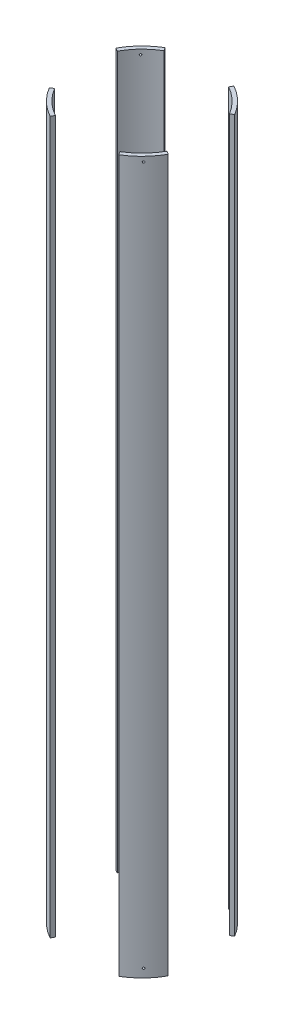
SolidWorks part; units mm, degrees
material "6061-T6 (SS)"
ref_plane "Front Plane" through (0, 0, 0) normal (0, 0, 1) x (1, 0, 0)
ref_plane "Top Plane" through (0, 0, 0) normal (0, 1, 0) x (1, 0, 0)
ref_plane "Right Plane" through (0, 0, 0) normal (1, 0, 0) x (0, 0, -1)
sketch "Sketch2" plane through (0, 0, 0) normal (0, 1, 0) x (1, 0, 0)
  circle A0 centre (0, 0) radius 88.9
  circle A1 centre (0, 0) radius 83.82
  dimension "D1" = 177.8
  dimension "D2" = 167.64
extrude "Boss-Extrude1" add sketch "Sketch2" along normal mid plane 935.896
sketch "Sketch3" plane through (0, 0, 0) normal (0, 1, 0) x (1, 0, 0)
  line L0 (0, 0) -> (169.6618, 101.6776)
  line L1 (-58.1167, 96.9749) -> (0, 0)
  line L2 (0, 0) -> (53.9, 96.9749)
  line L3 (53.9, 96.9749) -> (-58.1167, 96.9749)
  line L4 (0, 0) -> (70.9917, -118.4586)
  line L5 (70.9917, -118.4586) -> (-65.8409, -118.4586)
  line L6 (-65.8409, -118.4586) -> (0, 0)
  line L7 (169.6618, 101.6776) -> (169.6618, -94.3004)
  line L8 (169.6618, -94.3004) -> (0, 0)
  line L9 (0, 0) -> (-123.7413, 68.7771)
  line L10 (-123.7413, 68.7771) -> (-123.7413, -74.1577)
  line L11 (-123.7413, -74.1577) -> (0, 0)
  dimension "D1" = 60
  dimension "D2" = 60
  dimension "D3" = 60
  dimension "D4" = 60
  dimension "D5" = 30
  dimension "D6" = 30
extrude "Cut-Extrude1" cut sketch "Sketch3" against normal through all both and the other way through all contours L8 L7 L0 | L2 L3 L1 | L10 L11 L9 | L6 L5 L4
ref_plane "Bolt reference plane" through (-56.3092, 0, 58.1758) normal (0.6955, 0, -0.7185) x (-0.7185, 0, -0.6955)
sketch "Sketch5" plane through (-56.3092, 0, 58.1758) normal (0.6955, 0, -0.7185) x (-0.7185, 0, -0.6955)
  line L0 (-23.009, -467.948) -> (23.009, -467.948) construction
  circle A0 centre (-0.0228, 461.598) radius 1.27
  circle A1 centre (-0.0228, -456.8355) radius 1.27
  dimension "D1" = 2.54
  dimension "D4" = 11.1125
  dimension "D2" = 21.717
  dimension "D3" = 6.35
extrude "Bolt holes" cut sketch "Sketch5" against normal through all
pattern_circular "Bolt pattern" count 4 over 360 about axis through (0, 467.948, 0) along (0, 1, 0) of "Bolt holes"
equation "\"D1@Boss-Extrude1\"=3*12"
